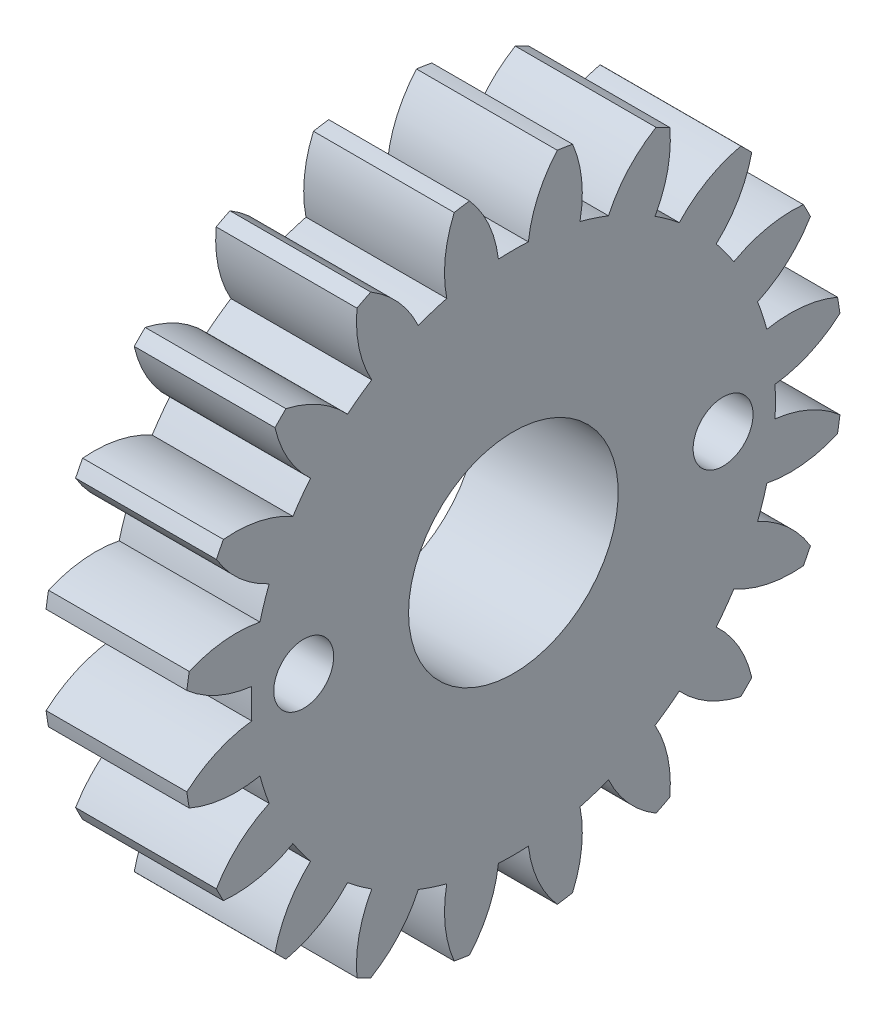
SolidWorks part; units mm, degrees
ref_plane "Plane1" through (0, 0, 0) normal (0, 0, 1) x (1, 0, 0)
ref_plane "Plane2" through (0, 0, 0) normal (0, 1, 0) x (1, 0, 0)
ref_plane "Plane3" through (0, 0, 0) normal (1, 0, 0) x (0, 0, -1)
other "Configuration Table"
sketch "HoldingSke" plane through (0, 0, 0) normal (0, 1, 0) x (1, 0, 0)
  line L0 (0, 0) -> (0.9397, -0.342)
  line L1 (-15, 0) -> (100, 0) construction
  line L2 (0, 0) -> (-2.1039, 2.3779)
  line L3 (0, 0) -> (-11.863, 4.5341)
  line L4 (0, 0) -> (8.1152, 2.9537)
  line L5 (0, 0) -> (-46.8476, -17.4728)
  line L6 (0, 0) -> (-4.1448, -2.7965)
  line L7 (-2.1039, 2.3779) -> (8.6586, 51.2059)
  line L8 (-76.2, 54.61) -> (-74.8, 54.61)
  line L9 (-71.009, 38.7566) -> (-53.1078, 45.2721)
  line L10 (-76.2, 71.12) -> (104.1128, 71.12)
  line L11 (0, 0) -> (-5, 0)
  line L12 (-76.2, 101.6) -> (-76.162, 101.6)
  line L13 (24.9733, 27.94) -> (52.9518, 28.4284)
  line L14 (24.9733, 27.94) -> (24.9743, 27.94)
  line L15 (24.9733, 27.94) -> (100.4006, 29.5858)
  line L16 (-63.627, -1) -> (-12.827, -1)
  circle A0 centre (0, 0) radius 4
  circle A1 centre (0, 0) radius 8.749
  circle A2 centre (0, 0) radius 37.5
  circle A3 centre (0, 0) radius 4
  dimension "MHD" = 17.498
  dimension "Hub_dia" = 75
  dimension "Bore" = 8
  dimension "MBD" = 8
  dimension "Num_teeth" = 20
  dimension "Pitch" = 1
  dimension "Overall_len" = 50
  dimension "Show_teeth" = 20
  dimension "Thickness" = 5
  dimension "OAL" = 50.0001
  dimension "T_dim" = 1.4
  dimension "Ap" = 20
  dimension "H" = 19.05
  dimension "Pitch_radius" = 180.3128
  dimension "Width" = 5
  dimension "Backlash" = 0.038
  dimension "Addendum_fac" = 1
  dimension "Dedendum_fac" = 1.25
  dimension "Clearance_fac" = 0.25
  dimension "Dedendum_add" = 0.001
  dimension "Module" = 1
sketch "BasProSke" plane through (0, 0, 0) normal (0, 1, 0) x (1, 0, 0)
  line L0 (-10, 0) -> (60, 0) construction
  line L1 (0, 0) -> (0, 11)
  line L2 (0, 0) -> (4.7, 0)
  line L3 (4.7, 0) -> (4.7, 11)
  line L4 (4.7, 11) -> (0, 11)
  dimension "Thickness" = 4.7
  dimension "Diameter" = 22
revolve "Base-Revolve" add sketch "BasProSke" angle 360 about L0
sketch "TooCutSke" plane through (0, 0, 0) normal (1, 0, 0) x (0, 0, -1)
  line L1 (0, 0) -> (0, 107) construction
  line L2 (0, 0) -> (-0.8511, 9.9637) construction
  line L3 (0, 0) -> (-3.1206, 19.7028) construction
  line L4 (-0.8511, 9.9637) -> (-1.5603, 9.8514) construction
  arc A0 (0.4999, 8.7347) -> (-0.4999, 8.7347) centre (0, 0) ccw
  arc A1 (1.4852, 10.9249) -> (-1.4852, 10.9249) centre (0, 0) ccw
  circle A2 centre (0, 0) radius 10 construction
  circle A3 centre (0, 0) radius 9.3969 construction
  arc A4 (-0.4999, 8.7347) -> (-1.4852, 10.9249) centre (-4.4722, 8.2645) ccw
  arc A5 (1.4852, 10.9249) -> (0.4999, 8.7347) centre (4.4722, 8.2645) ccw
  dimension "Root_dia" = 17.498
  dimension "Overcut_dia" = 22.0508
  dimension "Pitch_dia" = 20
  dimension "Base_dia" = 18.7939
  dimension "Flank_rad" = 4
  dimension "Half_ang" = 9
  dimension "Half_CT" = 0.7181
extrude "ToothCut" cut sketch "TooCutSke" along normal through all
fillet "Breaks" [suppressed] radius 0.02
fillet "RootFillets" [suppressed] radius 0.251
pattern_circular "TeethCuts" count 20 every 18 about axis through (-10, 0, 0) along (1, 0, 0) of "ToothCut", "RootFillets", "Breaks"
sketch "HubNeaOneSke" plane through (0, 0, 0) normal (-1, 0, 0) x (0, 0, 1)
  circle A0 centre (0, 0) radius 8.749
  dimension "Diameter" = 17.498
extrude "HubNearOne" [suppressed] add sketch "HubNeaOneSke" along normal blind 45.3001
sketch "HubNeaBotSke" plane through (0, 0, 0) normal (-1, 0, 0) x (0, 0, 1)
  circle A0 centre (0, 0) radius 8.749
  dimension "Diameter" = 17.498
extrude "HubNearBoth" [suppressed] add sketch "HubNeaBotSke" along normal blind 22.65
ref_plane "FarPln" through (4.7, 0, 0) normal (1, 0, 0) x (0, 0, -1)
sketch "HubFarSke" plane through (4.7, 0, 0) normal (1, 0, 0) x (0, 0, -1)
  circle A0 centre (0, 0) radius 8.749
  dimension "Diameter" = 17.498
extrude "HubFar" [suppressed] add sketch "HubFarSke" along normal blind 22.65
sketch "BorSke" plane through (0, 0, 0) normal (1, 0, 0) x (0, 0, -1)
  circle A0 centre (0, 0) radius 3.5
  dimension "Diameter" = 7
extrude "Bore" cut sketch "BorSke" along normal mid plane 100.0001
sketch "KeySke" plane through (0, 0, 0) normal (1, 0, 0) x (0, 0, -1)
  line L0 (-1.5, 0) -> (-1.5, 5.4)
  line L1 (-1.5, 5.4) -> (1.5, 5.4)
  line L2 (1.5, 5.4) -> (1.5, 0)
  line L3 (0, 0) -> (0, 34) construction
  line L4 (-1.5, 0) -> (1.5, 0)
  dimension "Offset" = 5.4
  dimension "Width" = 3
extrude "Keyway" [suppressed] cut sketch "KeySke" along normal mid plane 100.0001
pattern_circular "Keyway2" [suppressed] count 2 every 90 about axis through (-10, 0, 0) along (1, 0, 0)
sketch "Sketch1" plane through (4.7, 0, 0) normal (1, 0, 0) x (0, 0, -1)
  line L0 (-7, 0) -> (7, 0) construction
  circle A0 centre (-7, 0) radius 1
  circle A1 centre (7, 0) radius 1
  point P5 (0, 0)
  dimension "D1" = 2
  dimension "D2" = 2
extrude "Cut-Extrude1" cut sketch "Sketch1" against normal through all
equation "' \"Module@HoldingSke\" = 6.35"
equation "' \"Num_teeth@HoldingSke\" = 12"
equation "' \"Ap@HoldingSke\" =  20"
equation "' \"Ap@HoldingSke\" = 20"
equation "' \"Width@HoldingSke\" = 0.5 * 25.4"
equation "' \"Hub_dia@HoldingSke\"= 1 * 25.4"
equation "' \"Hub_dia@HoldingSke\" = 1 * 25.4"
equation "' \"Overall_len@HoldingSke\" = 1.0 * 25.4"
equation "' \"Bore@HoldingSke\" = 0.75 * 25.4"
equation "' \"T_dim@HoldingSke\" = 0.1 * 25.4"
equation "' \"Width@KeySke\" = 0.25 * 25.4"
equation "' \"Show_teeth@HoldingSke\" = 13"
equation "' \"Backlash@HoldingSke\" = 0.009 * 25.4"
equation "' \"Addendum_fac@HoldingSke\" = 1.0"
equation "' \"Dedendum_fac@HoldingSke\" = 1.25"
equation "' \"Dedendum_add@HoldingSke\" = 0.00005 * 25.4"
equation "' \"Clearance_fac@HoldingSke\" = 0.25"
equation "\"Pitch@HoldingSke\" = 1 / \"Module@HoldingSke\""
equation "\"Overcut_dia@TooCutSke\" = (\"Num_teeth@HoldingSke\" + 2 * \"Addendum_fac@HoldingSke\") / \"Pitch@HoldingSke\" + 0.002 * 25.4"
equation "\"Pitch_dia@TooCutSke\" = \"Num_teeth@HoldingSke\" / \"Pitch@HoldingSke\""
equation "\"Base_dia@TooCutSke\" = \"Num_teeth@HoldingSke\" / \"Pitch@HoldingSke\" * cos((\"Ap@HoldingSke\"  * 3.14159265 / 180))"
equation "\"Root_dia@TooCutSke\" = (\"Num_teeth@HoldingSke\" + 2) / \"Pitch@HoldingSke\" - 2 * (\"Addendum_fac@HoldingSke\" + \"Dedendum_fac@HoldingSke\") / \"Pitch@HoldingSke\" - \"Dedendum_add@HoldingSke\" * 2"
equation "\"Half_ang@TooCutSke\" = 180 / \"Num_teeth@HoldingSke\""
equation "\"Half_CT@TooCutSke\" = \"Num_teeth@HoldingSke\" / \"Pitch@HoldingSke\" * sin((3.14159265 / 2 / \"Num_teeth@HoldingSke\")) / 2 - 7 * \"Backlash@HoldingSke\" / 4"
equation "\"Flank_rad@TooCutSke\" = \"Num_teeth@HoldingSke\" / \"Pitch@HoldingSke\" / 5"
equation "\"Radius@RootFillets\" = \"Clearance_fac@HoldingSke\" / \"Pitch@HoldingSke\" + \"Dedendum_add@HoldingSke\""
equation "\"Break_rad@Breaks\" = 0.02 / \"Pitch@HoldingSke\""
equation "\"Thickness@HoldingSke\" = \"Width@HoldingSke\""
equation "\"OAL@HoldingSke\" = \"Thickness@HoldingSke\""
equation "\"MHD@HoldingSke\" = (\"Num_teeth@HoldingSke\" + 2) / \"Pitch@HoldingSke\" - 2 * (\"Addendum_fac@HoldingSke\" + \"Dedendum_fac@HoldingSke\")  / \"Pitch@HoldingSke\" - \"Dedendum_add@HoldingSke\" * 2"
equation "\"MBD@HoldingSke\" = (\"Num_teeth@HoldingSke\" + 2) / \"Pitch@HoldingSke\" - 2 * (\"Addendum_fac@HoldingSke\" + \"Dedendum_fac@HoldingSke\")  / \"Pitch@HoldingSke\" - \"Dedendum_add@HoldingSke\" * 2 - 0.002 * 25.4"
equation "\"MHD@HoldingSke\" = ((sgn( \"MHD@HoldingSke\" - \"Hub_dia@HoldingSke\" )-1)*( \"MHD@HoldingSke\" - \"Hub_dia@HoldingSke\" ))/-2+ \"Hub_dia@HoldingSke\""
equation "\"MBD@HoldingSke\" = ((sgn( \"MBD@HoldingSke\" - \"Bore@HoldingSke\" )-1)*( \"MBD@HoldingSke\" - \"Bore@HoldingSke\" ))/-2+ \"Bore@HoldingSke\""
equation "\"OAL@HoldingSke\" = ((sgn( \"OAL@HoldingSke\" - \"Overall_len@HoldingSke\" )+1)*( \"OAL@HoldingSke\" - \"Overall_len@HoldingSke\" ))/2 + \"Overall_len@HoldingSke\" + 0.000002 * 25.4"
equation "\"Num_teeth@TeethCuts\" = int( \"Show_teeth@HoldingSke\" ) + 1"
equation "\"Num_teeth@TeethCuts\" = ((sgn( \"Num_teeth@TeethCuts\" - \"Num_teeth@HoldingSke\" )-1)*( \"Num_teeth@TeethCuts\" - \"Num_teeth@HoldingSke\" ))/-2+ \"Num_teeth@HoldingSke\""
equation "\"Num_teeth@TeethCuts\" = ((sgn( \"Num_teeth@TeethCuts\" - 2.0)+1)*( \"Num_teeth@TeethCuts\" - 2.0))/2 +2.0"
equation "\"Angle@TeethCuts\" = 360.0 / \"Num_teeth@HoldingSke\""
equation "\"Diameter@BasProSke\" = (\"Num_teeth@HoldingSke\" + 2 * \"Addendum_fac@HoldingSke\") / \"Pitch@HoldingSke\""
equation "' \"Fillet_rad@BasProSke\" =  \"Thickness@HoldingSke\" * 0.05"
equation "' \"Fillet_rad@BasProSke\" = \"Thickness@HoldingSke\" * 0.05"
equation "\"MHD@HoldingSke\" = ((sgn( \"MHD@HoldingSke\" - \"Root_dia@TooCutSke\" )-1)*( \"MHD@HoldingSke\" - \"Root_dia@TooCutSke\" ))/-2+ \"Root_dia@TooCutSke\""
equation "\"Diameter@HubNeaOneSke\" = \"MHD@HoldingSke\""
equation "\"Length@HubNearOne\" = \"OAL@HoldingSke\" - \"Thickness@BasProSke\""
equation "\"Diameter@HubNeaBotSke\" = \"MHD@HoldingSke\""
equation "\"Length@HubNearBoth\" = ( \"OAL@HoldingSke\" - \"Thickness@BasProSke\" ) / 2.0"
equation "\"Thickness@FarPln\" = \"Thickness@BasProSke\""
equation "\"Diameter@HubFarSke\" = \"MHD@HoldingSke\""
equation "\"Length@HubFar\" = ( \"OAL@HoldingSke\" - \"Thickness@BasProSke\" ) / 2.0"
equation "\"D1@Bore\" = \"OAL@HoldingSke\" * 2.0"
equation "\"D1@Keyway\" = \"OAL@HoldingSke\" * 2.0"
equation "\"Offset@KeySke\" = \"T_dim@HoldingSke\" + \"MBD@HoldingSke\" / 2.0"
